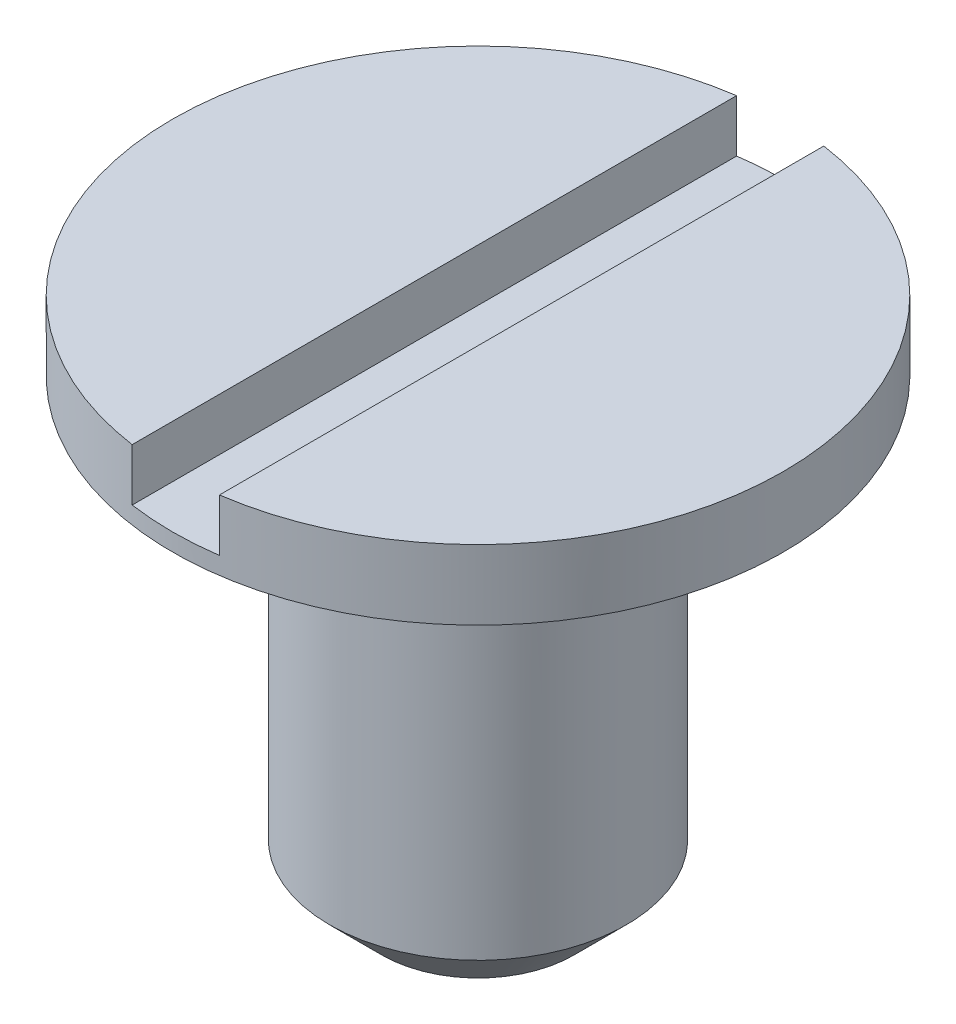
SolidWorks part; units mm, degrees
ref_plane "Front Plane" through (0, 0, 0) normal (0, 0, 1) x (1, 0, 0)
ref_plane "Top Plane" through (0, 0, 0) normal (0, 1, 0) x (1, 0, 0)
ref_plane "Right Plane" through (0, 0, 0) normal (1, 0, 0) x (0, 0, -1)
sketch "Sketch1" plane through (0, 0, 0) normal (0, 1, 0) x (1, 0, 0)
  circle A0 centre (0, 0) radius 1.75
  dimension "D1" = 3.5
extrude "Boss-Extrude1" add sketch "Sketch1" along normal blind 3
sketch "Sketch2" plane through (0, 0, 0) normal (0, 0, 1) x (1, 0, 0)
  line L0 (0, 0) -> (0, 3) construction
  line L1 (1.75, 3) -> (-1.75, 3) construction
  line L2 (1.75, 0) -> (1.75, 3) construction
  line L3 (1.75, 2.6) -> (0.85, 2.6)
  line L4 (1.75, 2.6) -> (1.75, 0)
  line L5 (1.75, 0) -> (0.85, 0)
  line L6 (0.85, 2.6) -> (0.85, 0)
  dimension "D1" = 1.7
  dimension "D2" = 0.4
revolve "Cut-Revolve1" cut sketch "Sketch2" angle 360 about L0
cosmetic thread "Cosmetic Thread1" parameters "D1"=2.1, "D2"=1.4
sketch "Sketch3" plane through (0, 3, 0) normal (0, 1, 0) x (1, 0, 0)
  line L1 (-0.25, -1.85) -> (0.25, -1.85)
  line L2 (-0.25, -1.85) -> (-0.25, 1.85)
  line L3 (-0.25, 1.85) -> (0.25, 1.85)
  line L4 (0.25, -1.85) -> (0.25, 1.85)
  line L5 (-0.25, -1.85) -> (0.25, 1.85) construction
  line L6 (-0.25, 1.85) -> (0.25, -1.85) construction
  circle A0 centre (0, 0) radius 1.75 construction
  point P0 (0, 0)
  dimension "D2" = 0.1
  dimension "D1" = 0.5
extrude "Cut-Extrude1" cut sketch "Sketch3" against normal blind 0.3
chamfer "Chamfer1" distance 0.3 angle 45 1 edges at (0, 0, -0.85)
